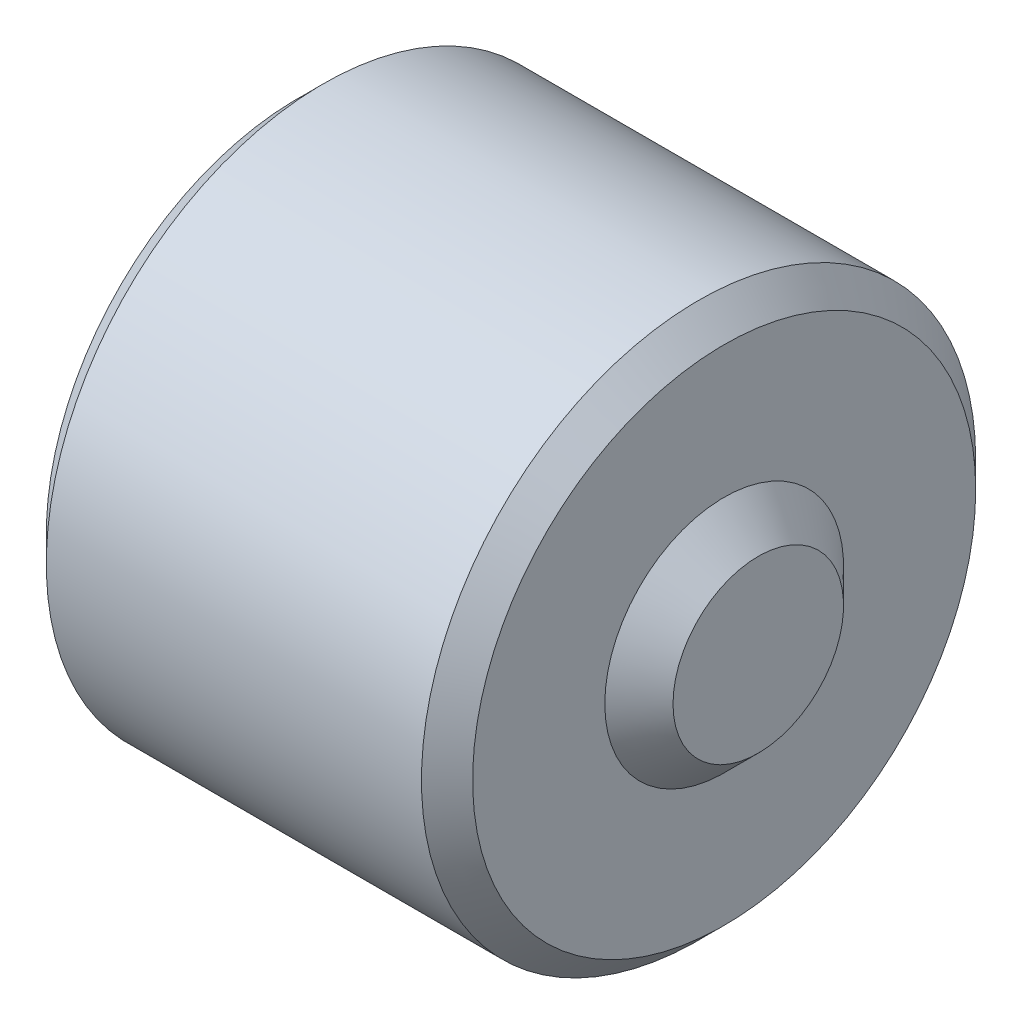
SolidWorks part; units mm, degrees
material "1060 Alloy"
ref_plane "Front Plane" through (0, 0, 0) normal (0, 0, 1) x (1, 0, 0)
ref_plane "Top Plane" through (0, 0, 0) normal (0, 1, 0) x (1, 0, 0)
ref_plane "Right Plane" through (0, 0, 0) normal (1, 0, 0) x (0, 0, -1)
other "Configuration Table"
sketch "Sketch1" plane through (0, 0, 0) normal (1, 0, 0) x (0, 0, -1)
  circle A1 centre (0, 0) radius 8.255
  dimension "D2" = 16.51
extrude "Boss-Extrude1" add sketch "Sketch1" against normal blind 12.7
sketch "Sketch2" plane through (-12.7, 0, 0) normal (-1, 0, 0) x (0, 0, 1)
  circle A0 centre (0, 0) radius 5.715
  dimension "D1" = 11.43
extrude "Cut-Extrude1" cut sketch "Sketch2" against normal blind 10.16
chamfer "Chamfer1" distance 0.762 angle 45 2 edges at (-12.7, 0, -8.255) (0, 0, -8.255)
ref_axis "Axis1" through (-11.938, 0, 0) along (1, 0, 0)
sketch "Sketch3" plane through (0, 0, 0) normal (0, 1, 0) x (1, 0, 0)
  line L0 (0, 0) -> (1.016, 0)
  line L1 (1.016, 0) -> (1.016, 2.54)
  line L2 (1.016, 2.54) -> (0, 3.556)
  line L3 (0, -7.493) -> (0, 7.493) construction
  line L4 (0, 3.556) -> (0, 0)
  dimension "D1" = 1.016
  dimension "D2" = 2.54
  dimension "D3" = 45
revolve "Revolve1" add sketch "Sketch3" angle 360 about axis through (-11.938, 0, 0) along (1, 0, 0)
